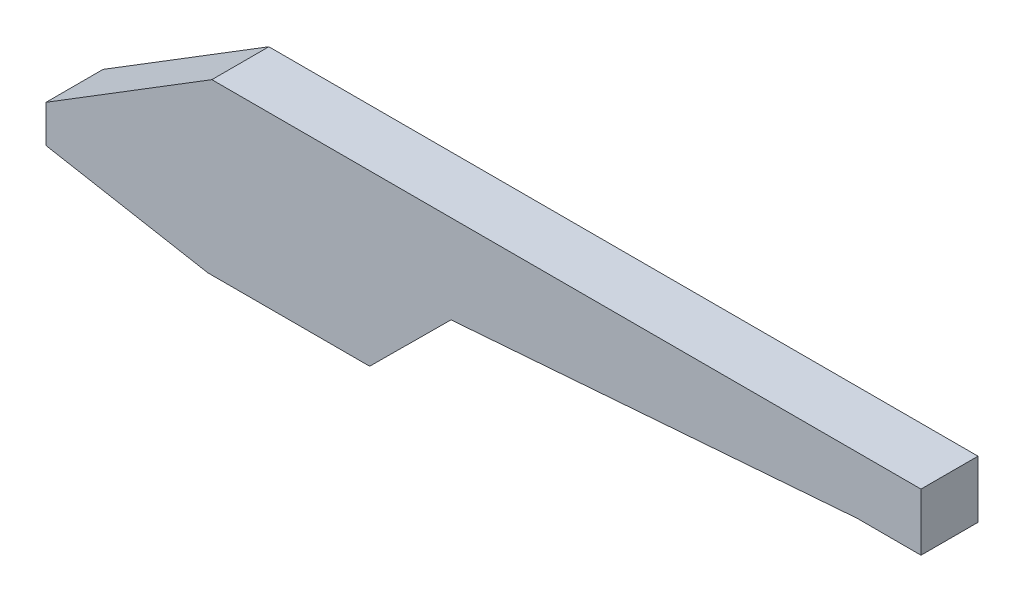
SolidWorks part; units mm, degrees
ref_plane "Front Plane" through (0, 0, 0) normal (0, 0, 1) x (1, 0, 0)
ref_plane "Top Plane" through (0, 0, 0) normal (0, 1, 0) x (1, 0, 0)
ref_plane "Right Plane" through (0, 0, 0) normal (1, 0, 0) x (0, 0, -1)
sketch "Sketch1" plane through (0, 0, 0) normal (0, 0, 1) x (1, 0, 0)
  line L0 (576.5303, 118.8135) -> (-381.2461, 118.8135)
  line L7 (576.5303, 118.8135) -> (614.0166, 118.8135)
  line L8 (614.0166, 118.8135) -> (614.0166, 38.3698)
  line L9 (614.0166, 38.3698) -> (524.5772, 38.4839)
  line L10 (524.5772, 38.4839) -> (-45.5744, -5.3355)
  line L11 (-45.5744, -5.3355) -> (-159.8023, -118.8135)
  line L12 (-159.8023, -118.8135) -> (-386.9095, -118.8135)
  line L13 (-614.0166, -77.6682) -> (-614.0166, -25.1061)
  line L14 (-614.0166, -25.1061) -> (-381.2461, 118.8135)
  line L15 (-386.9095, -118.8135) -> (-614.0166, -77.6682)
  point P0 (0, 0)
extrude "Boss-Extrude1" add sketch "Sketch1" along normal mid plane 80
